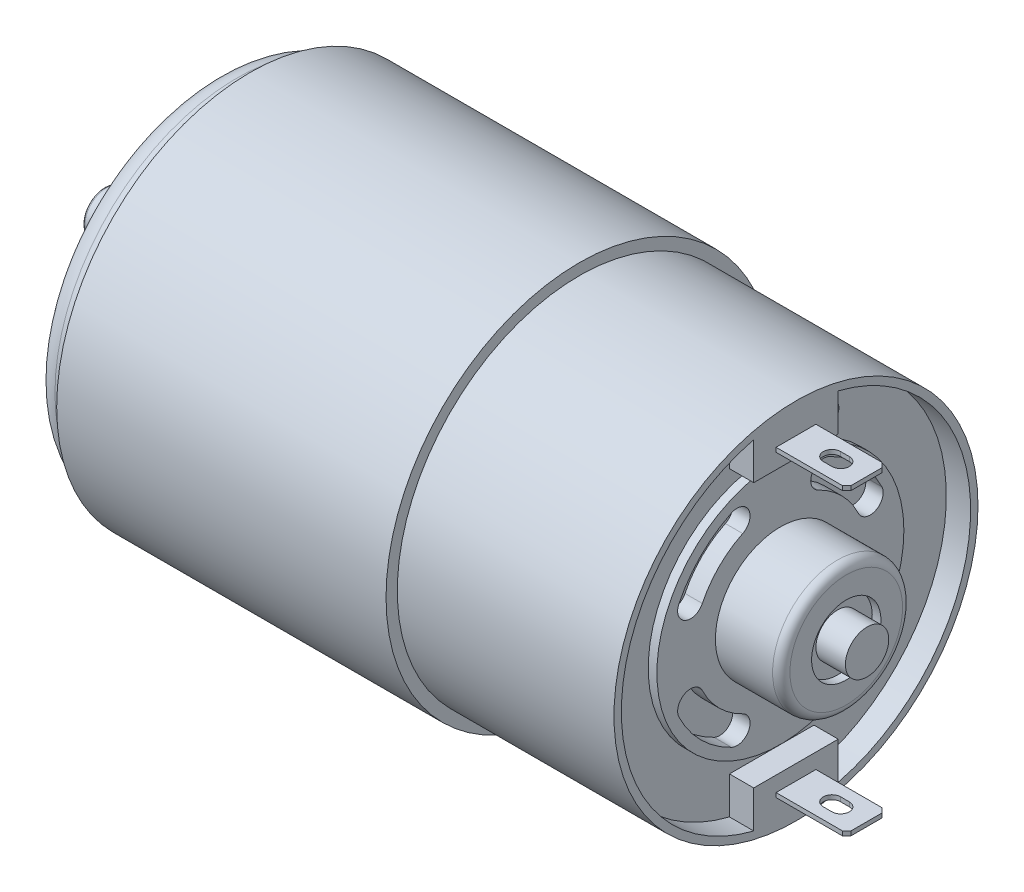
SolidWorks part; units mm, degrees
ref_plane "Front Plane" through (0, 0, 0) normal (0, 0, 1) x (1, 0, 0)
ref_plane "Top Plane" through (0, 0, 0) normal (0, 1, 0) x (1, 0, 0)
ref_plane "Right Plane" through (0, 0, 0) normal (1, 0, 0) x (0, 0, -1)
sketch "Sketch1" plane through (0, 0, 0) normal (0, 0, 1) x (1, 0, 0)
  line L0 (4, 22.3) -> (4, 0)
  line L1 (4, 0) -> (42, 0)
  line L2 (42, 0) -> (42, 22.3)
  line L3 (42, 22.3) -> (4, 22.3)
  line L4 (4, 0) -> (42, 0) construction
revolve "Revolve1" add sketch "Sketch1" angle 360 about L4
sketch "Sketch2" plane through (42, 0, 0) normal (1, 0, 0) x (0, 0, -1)
  circle A0 centre (0, 0) radius 21
extrude "Boss-Extrude1" add sketch "Sketch2" along normal blind 25
sketch "Sketch3" plane through (67, 0, 0) normal (1, 0, 0) x (0, 0, -1)
  line L0 (-2.3, 17) -> (-2.3, 17.5)
  line L1 (-2.3, 17.5) -> (2.3, 17.5)
  line L2 (2.3, 17.5) -> (2.3, 17)
  line L3 (2.3, 17) -> (-2.3, 17)
extrude "Boss-Extrude2" add sketch "Sketch3" along normal blind 8.15
sketch "Sketch4" plane through (0, 17.5, 0) normal (0, 1, 0) x (-1, 0, 0)
  line L0 (-72.15, -1) -> (-71.15, -1)
  line L1 (-71.15, 1) -> (-72.15, 1)
  arc A0 (-71.15, -1) -> (-71.15, 1) centre (-71.15, 0) ccw
  arc A1 (-72.15, 1) -> (-72.15, -1) centre (-72.15, 0) ccw
extrude "Cut-Extrude1" cut sketch "Sketch4" against normal through all
sketch "Sketch5" plane through (67, 0, 0) normal (1, 0, 0) x (0, 0, -1)
  line L0 (-2.3, -17.5) -> (-2.3, -17)
  line L1 (-2.3, -17) -> (2.3, -17)
  line L2 (2.3, -17) -> (2.3, -17.5)
  line L3 (2.3, -17.5) -> (-2.3, -17.5)
extrude "Boss-Extrude3" add sketch "Sketch5" along normal blind 8.15
sketch "Sketch6" plane through (0, -17.5, 0) normal (0, -1, 0) x (1, 0, 0)
  line L0 (72.15, 1) -> (71.15, 1)
  line L1 (71.15, -1) -> (72.15, -1)
  arc A0 (71.15, 1) -> (71.15, -1) centre (71.15, 0) ccw
  arc A1 (72.15, -1) -> (72.15, 1) centre (72.15, 0) ccw
extrude "Cut-Extrude2" cut sketch "Sketch6" against normal up to next
sketch "Sketch7" plane through (67, 0, 0) normal (1, 0, 0) x (0, 0, -1)
  line L0 (4.875, 19.5514) -> (4.875, 15.25)
  line L1 (4.875, 15.25) -> (-4.875, 15.25)
  line L2 (-4.875, 15.25) -> (-4.875, 19.5514)
  line L3 (-4.875, -19.5514) -> (-4.875, -15.25)
  line L4 (-4.875, -15.25) -> (4.875, -15.25)
  line L5 (4.875, -15.25) -> (4.875, -19.5514)
  arc A0 (-4.875, 19.5514) -> (-4.875, -19.5514) centre (0, 0) ccw
  arc A1 (4.875, -19.5514) -> (4.875, 19.5514) centre (0, 0) ccw
extrude "Cut-Extrude3" cut sketch "Sketch7" against normal blind 2.8
sketch "Sketch8" plane through (64.2, 0, 0) normal (1, 0, 0) x (0, 0, -1)
  circle A0 centre (0, 0) radius 14.25
extrude "Boss-Extrude4" add sketch "Sketch8" along normal blind 1
sketch "Sketch9" plane through (65.2, 0, 0) normal (1, 0, 0) x (0, 0, -1)
  arc A0 (-5.6522, 11.707) -> (-11.707, 5.6522) centre (0, 0) ccw
  arc A1 (-11.707, 5.6522) -> (-9.0054, 4.3478) centre (-10.3562, 5) ccw
  arc A2 (-9.0054, 4.3478) -> (-4.3478, 9.0054) centre (0, 0) cw
  arc A3 (-4.3478, 9.0054) -> (-5.6522, 11.707) centre (-5, 10.3562) ccw
extrude "Cut-Extrude4" cut sketch "Sketch9" against normal blind 2
sketch "Sketch10" plane through (65.2, 0, 0) normal (1, 0, 0) x (0, 0, -1)
  arc A0 (11.707, 5.6522) -> (5.6522, 11.707) centre (0, 0) ccw
  arc A1 (5.6522, 11.707) -> (4.3478, 9.0054) centre (5, 10.3562) ccw
  arc A2 (4.3478, 9.0054) -> (9.0054, 4.3478) centre (0, 0) cw
  arc A3 (9.0054, 4.3478) -> (11.707, 5.6522) centre (10.3562, 5) ccw
extrude "Cut-Extrude5" cut sketch "Sketch10" against normal blind 2
sketch "Sketch11" plane through (65.2, 0, 0) normal (1, 0, 0) x (0, 0, -1)
  arc A0 (5.6522, -11.707) -> (11.707, -5.6522) centre (0, 0) ccw
  arc A1 (11.707, -5.6522) -> (9.0054, -4.3478) centre (10.3562, -5) ccw
  arc A2 (9.0054, -4.3478) -> (4.3478, -9.0054) centre (0, 0) cw
  arc A3 (4.3478, -9.0054) -> (5.6522, -11.707) centre (5, -10.3562) ccw
extrude "Cut-Extrude6" cut sketch "Sketch11" against normal blind 2
sketch "Sketch12" plane through (65.2, 0, 0) normal (1, 0, 0) x (0, 0, -1)
  arc A0 (-11.707, -5.6522) -> (-5.6522, -11.707) centre (0, 0) ccw
  arc A1 (-5.6522, -11.707) -> (-4.3478, -9.0054) centre (-5, -10.3562) ccw
  arc A2 (-4.3478, -9.0054) -> (-9.0054, -4.3478) centre (0, 0) cw
  arc A3 (-9.0054, -4.3478) -> (-11.707, -5.6522) centre (-10.3562, -5) ccw
extrude "Cut-Extrude7" cut sketch "Sketch12" against normal blind 2
sketch "Sketch13" plane through (4, 0, 0) normal (-1, 0, 0) x (0, 0, 1)
  circle A0 centre (0, 0) radius 21
extrude "Boss-Extrude5" add sketch "Sketch13" along normal blind 4
sketch "Sketch14" plane through (0, 0, 0) normal (-1, 0, 0) x (0, 0, 1)
  line L0 (6.7619, 14.5009) -> (4.7756, 10.2413)
  line L1 (10.2413, 4.7756) -> (14.5009, 6.7619)
  arc A0 (14.5009, 6.7619) -> (6.7619, 14.5009) centre (0, 0) ccw
  arc A1 (4.7756, 10.2413) -> (10.2413, 4.7756) centre (0, 0) cw
extrude "Cut-Extrude8" cut sketch "Sketch14" against normal blind 10
sketch "Sketch15" plane through (0, 0, 0) normal (-1, 0, 0) x (0, 0, 1)
  line L0 (-6.7619, -14.5009) -> (-4.7756, -10.2413)
  line L1 (-10.2413, -4.7756) -> (-14.5009, -6.7619)
  arc A0 (-14.5009, -6.7619) -> (-6.7619, -14.5009) centre (0, 0) ccw
  arc A1 (-4.7756, -10.2413) -> (-10.2413, -4.7756) centre (0, 0) cw
extrude "Cut-Extrude9" cut sketch "Sketch15" against normal blind 10
sketch "Sketch16" plane through (0, 0, 0) normal (-1, 0, 0) x (0, 0, 1)
  line L0 (-14.5009, 6.7619) -> (-10.2413, 4.7756)
  line L1 (-4.7756, 10.2413) -> (-6.7619, 14.5009)
  arc A0 (-6.7619, 14.5009) -> (-14.5009, 6.7619) centre (0, 0) ccw
  arc A1 (-10.2413, 4.7756) -> (-4.7756, 10.2413) centre (0, 0) cw
extrude "Cut-Extrude10" cut sketch "Sketch16" against normal blind 10
sketch "Sketch17" plane through (0, 0, 0) normal (-1, 0, 0) x (0, 0, 1)
  line L0 (14.5009, -6.7619) -> (10.2413, -4.7756)
  line L1 (4.7756, -10.2413) -> (6.7619, -14.5009)
  arc A0 (6.7619, -14.5009) -> (14.5009, -6.7619) centre (0, 0) ccw
  arc A1 (10.2413, -4.7756) -> (4.7756, -10.2413) centre (0, 0) cw
extrude "Cut-Extrude11" cut sketch "Sketch17" against normal blind 10
sketch "Sketch18" plane through (65.2, 0, 0) normal (1, 0, 0) x (0, 0, -1)
  circle A0 centre (0, 0) radius 7.5
extrude "Boss-Extrude6" add sketch "Sketch18" along normal blind 7.6
hole_wizard "Ø8.0 (8) Diameter Hole1" positions "Sketch20" profile "Sketch19" hole size "Ø8.0" standard "ANSI Metric"
sketch "Sketch20" plane through (72.8, 0, 0) normal (1, 0, 0) x (0, 0, -1)
  point P0 (0, 0)
sketch "Sketch19" plane through (72.8, 0, 0) normal (0, 1, 0) x (0, 0, -1)
  line L0 (0, 0) -> (0, 1)
  line L1 (0, 1) -> (4, 1)
  line L2 (4, 1) -> (4, 0)
  line L5 (4, 0) -> (0, 0)
  line L10 (0, 1) -> (-4, 1) construction
  line L11 (0, -6.35) -> (0, 107.95) construction
  dimension "Hole Dia." = 8
  dimension "Hole Depth" = 1
  dimension "Drill Angle" = 180
sketch "Sketch21" plane through (0, 0, 0) normal (-1, 0, 0) x (0, 0, 1)
  circle A0 centre (0, 0) radius 8.65
extrude "Boss-Extrude7" add sketch "Sketch21" along normal blind 5
hole_wizard "M12 Clearance Hole1" positions "Sketch23" profile "Sketch22" hole size "M12" standard "ANSI Metric"
sketch "Sketch23" plane through (-5, 0, 0) normal (-1, 0, 0) x (0, 0, 1)
  point P0 (0, 0)
sketch "Sketch22" plane through (-5, 0, 0) normal (0, 1, 0) x (0, 0, 1)
  line L0 (0, 0) -> (0, 1)
  line L1 (0, 1) -> (6.625, 1)
  line L2 (6.625, 1) -> (6.625, 0)
  line L5 (6.625, 0) -> (0, 0)
  line L10 (0, 1) -> (-6.625, 1) construction
  line L11 (0, -6.35) -> (0, 107.95) construction
  dimension "Hole Dia." = 13.25
  dimension "Hole Depth" = 1
  dimension "Drill Angle" = 180
ref_plane "Plane1" through (0, 0, 0) normal (0, 0, -1) x (-1, 0, 0)
sketch "Sketch24" plane through (0, 0, 0) normal (0, 0, -1) x (-1, 0, 0)
  line L0 (4, 3.75) -> (4, 0)
  line L1 (4, 0) -> (12.8, 0)
  line L2 (12.8, 0) -> (12.8, 2.5)
  line L3 (12.8, 2.5) -> (5, 2.5)
  line L4 (5, 2.5) -> (5, 3.75)
  line L5 (5, 3.75) -> (4, 3.75)
  line L6 (4, 0) -> (12.8, 0) construction
revolve "Revolve2" add sketch "Sketch24" angle 360 about L6
sketch "Sketch25" plane through (0, 0, 0) normal (0, 0, -1) x (-1, 0, 0)
  line L0 (-75.2, 2.5) -> (-75.2, 0)
  line L1 (-75.2, 0) -> (-71.8, 0)
  line L2 (-71.8, 0) -> (-71.8, 2.5)
  line L3 (-71.8, 2.5) -> (-75.2, 2.5)
  line L4 (-75.2, 0) -> (-71.8, 0) construction
revolve "Revolve3" add sketch "Sketch25" angle 360 about L4
hole_wizard "Ø2.5 (2.5) Diameter Hole1" positions "Sketch27" profile "Sketch26" hole size "Ø2.5" standard "ANSI Metric"
sketch "Sketch27" plane through (64.2, 0, 0) normal (1, 0, 0) x (0, 0, -1)
  point P0 (6.5, 15)
sketch "Sketch26" plane through (64.2, 15, -6.5) normal (0, 1, 0) x (0, 0, -1)
  line L0 (0, 0) -> (0, 0.1)
  line L1 (0, 0.1) -> (1.25, 0.1)
  line L2 (1.25, 0.1) -> (1.25, 0)
  line L5 (1.25, 0) -> (0, 0)
  line L10 (0, 0.1) -> (-1.25, 0.1) construction
  line L11 (0, -6.35) -> (0, 107.95) construction
  dimension "Hole Dia." = 2.5
  dimension "Hole Depth" = 0.1
  dimension "Drill Angle" = 180
hole_wizard "Ø3.3 (3.3) Diameter Hole1" positions "Sketch29" profile "Sketch28" hole size "Ø3.3" standard "ANSI Metric"
sketch "Sketch29" plane through (0, 0, 0) normal (-1, 0, 0) x (0, 0, 1)
  point P0 (0, 14.5)
  point P1 (0, -14.5)
sketch "Sketch28" plane through (0, 14.5, 0) normal (0, 1, 0) x (0, 0, 1)
  line L0 (0, 0) -> (0, 12.4914)
  line L1 (0, 12.4914) -> (1.65, 11.5)
  line L2 (1.65, 11.5) -> (1.65, 0)
  line L5 (1.65, 0) -> (0, 0)
  line L10 (0, 12.4914) -> (-1.65, 11.5) construction
  line L11 (0, -6.35) -> (0, 107.95) construction
  dimension "Hole Dia." = 3.3
  dimension "Hole Depth" = 11.5
  dimension "Drill Angle" = 118
chamfer "Chamfer1" distance 0.5 angle 45 4 edges at (75.15, 17.25, 2.3) (75.15, -17.25, -2.3) (75.15, 17.25, -2.3) (75.15, -17.25, 2.3)
fillet "Fillet1" radius 0.25 1 edges at (-12.8, 0, 2.5)
fillet "Fillet2" radius 0.75 1 edges at (-5, 0, 8.65)
fillet "Fillet3" radius 1 1 edges at (72.8, 0, -7.5)
fillet "Fillet4" radius 2.5 1 edges at (0, 0, 21)
